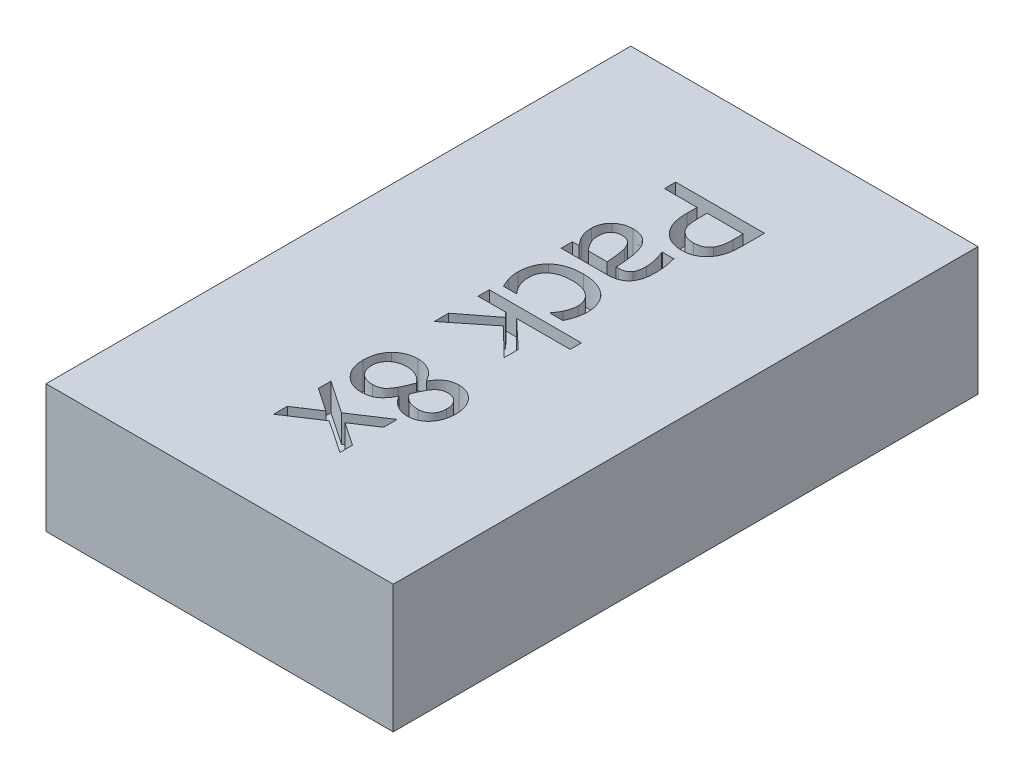
SolidWorks part; units mm, degrees
material "Rubber"
ref_plane "Спереди" through (0, 0, 0) normal (0, 0, 1) x (1, 0, 0)
ref_plane "Сверху" through (0, 0, 0) normal (0, 1, 0) x (1, 0, 0)
ref_plane "Справа" through (0, 0, 0) normal (1, 0, 0) x (0, 0, -1)
sketch "Sketch1" plane through (0, 0, 0) normal (0, 0, 1) x (1, 0, 0)
  line L1 (-19, -7) -> (19, -7)
  line L2 (-19, -7) -> (-19, 7)
  line L3 (-19, 7) -> (19, 7)
  line L4 (19, -7) -> (19, 7)
  line L5 (-19, -7) -> (19, 7) construction
  line L6 (-19, 7) -> (19, -7) construction
  point P0 (0, 0)
  dimension "D1" = 38
  dimension "D2" = 14
extrude "Boss-Extrude1" add sketch "Sketch1" along normal blind 64
sketch "Sketch2" plane through (0, 7, 0) normal (0, 1, 0) x (1, 0, 0)
  line L0 (-3.6534, 0) -> (-3.6534, -64) construction
  line L1 (19, 0) -> (-19, 0) construction
  line L2 (19, -64) -> (-19, -64) construction
  text T0 "Pack 8x" font "Tahoma" height in points 36
extrude "Cut-Extrude1" cut sketch "Sketch2" against normal blind 3
